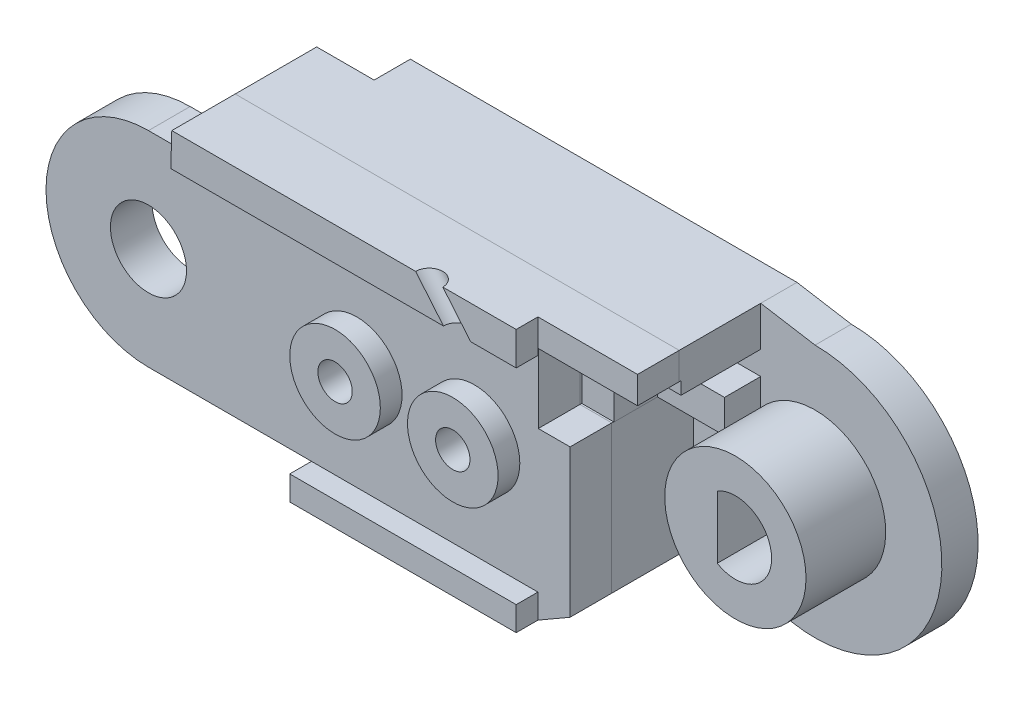
SolidWorks part; units mm, degrees
ref_plane "Front Plane" through (0, 0, 0) normal (0, 0, 1) x (1, 0, 0)
ref_plane "Top Plane" through (0, 0, 0) normal (0, 1, 0) x (1, 0, 0)
ref_plane "Right Plane" through (0, 0, 0) normal (1, 0, 0) x (0, 0, -1)
sketch "Sketch3" plane through (0, 0, 0) normal (0, 0, 1) x (1, 0, 0)
  line L7 (8, 0) -> (9, -2.5)
  line L11 (30, 7) -> (27, 7.5)
  line L13 (0, 7) -> (0, 7.5) construction
  line L14 (0, 7.5) -> (-22.3287, 7.5) construction
  line L15 (0, 5.3) -> (-14, 5.3) construction
  line L16 (0, 4) -> (-14, 4) construction
  line L17 (-14, 4) -> (-14, 5.3) construction
  line L18 (5.6569, 5.6569) -> (5.6569, 7.5)
  line L19 (5.6569, 7.5) -> (27, 7.5)
  line L20 (21.5, -7) -> (9, -7)
  line L21 (9, -7) -> (9, -2.5)
  line L23 (25.0503, -4.9497) -> (21.5, -7)
  arc A4 (8, 0) -> (5.6569, 5.6569) centre (0, 0) ccw
  arc A5 (25.0503, -4.9497) -> (30, 7) centre (30, 0) ccw
  circle A6 centre (0, 0) radius 7 construction
  circle A7 centre (0, 0) radius 3.9 construction
  circle A8 centre (0, 0) radius 5.3 construction
  circle A9 centre (0, 0) radius 4 construction
  dimension "D10" = 0.5
  dimension "D17" = 14
  dimension "D5" = 135
  dimension "D6" = 12.5
  dimension "D7" = 4.5
  dimension "D8" = 1
  dimension "D9" = 45
  dimension "D11" = 1.8431
  dimension "D12" = 30
  dimension "D14" = 3
extrude "Boss-Extrude1" add sketch "Sketch3" along normal blind 2 contours A5 L11 L19 L18 A4 L7 L21 L20 L23
sketch "Sketch20" plane through (0, 0, 0) normal (0, 0, 1) x (1, 0, 0)
  line L0 (0, 7) -> (0, 7.5) construction
  line L1 (0, 7.5) -> (-19.4737, 7.5) construction
  line L2 (0, 5.3) -> (-14, 5.3) construction
  line L3 (0, 4) -> (-14, 4) construction
  line L4 (-14, 4) -> (-14, 5.3) construction
  line L5 (0, 5.3) -> (17.4849, 5.3) construction
  line L6 (17.4849, 5.3) -> (17.4849, 4) construction
  line L7 (17.4849, 4) -> (0, 4) construction
  line L8 (-2.5, 7.5) -> (-2.5, 2.868) construction
  circle A0 centre (0, 0) radius 7 construction
  circle A1 centre (0, 0) radius 3.9 construction
  circle A3 centre (0, 0) radius 5.3 construction
  circle A4 centre (0, 0) radius 4 construction
  circle A5 centre (0, 0) radius 2 construction
  dimension "D1" = 0
  dimension "D2" = 2.5
ref_plane "Plane1" through (0, 0, 2) normal (0, 0, 1) x (1, 0, 0)
sketch "Sketch4" plane through (0, 0, 2) normal (0, 0, 1) x (1, 0, 0)
  line L4 (5.6569, 5.6569) -> (5.6569, 7.5)
  line L5 (5.6569, 5.6569) -> (5.6569, 7.5) construction
  line L6 (5.6569, 7.5) -> (21.5, 7.5)
  line L10 (8, 0) -> (9, -2.5)
  line L11 (9, -2.5) -> (9, -7)
  line L12 (9, -7) -> (21.5, -7)
  line L13 (21.5, -7) -> (21.5, 7.5)
  arc A0 (8, 0) -> (5.6569, 5.6569) centre (0, 0) ccw construction
  arc A3 (8, 0) -> (5.6569, 5.6569) centre (0, 0) ccw
sketch "Sketch22" plane through (0, 0, 2) normal (0, 0, 1) x (1, 0, 0)
  line L0 (5.6569, 5.6569) -> (2.4868, 5.6569)
  line L1 (5.6569, 7.5) -> (21.5, 7.5)
  line L2 (5.6569, 7.5) -> (2.4868, 7.5)
  line L3 (2.4868, 7.5) -> (2.4868, 5.6569)
  line L6 (8, 0) -> (9, -2.5)
  line L7 (9, -2.5) -> (9, -7)
  line L8 (9, -7) -> (21.5, -7)
  line L10 (21.5, 7.5) -> (27, 7.5)
  line L11 (27, 7.5) -> (27, 2.172)
  line L12 (27, 2.172) -> (23.2751, 2.172)
  line L13 (21.5, -7) -> (23.2751, -5.9749)
  line L14 (25.0503, -4.9497) -> (21.5, -7) construction
  line L15 (23.2751, -5.9749) -> (23.2751, 2.172)
  arc A0 (8, 0) -> (5.6569, 5.6569) centre (0, 0) ccw
extrude "Boss-Extrude6" add sketch "Sketch22" along normal blind 4.5
sketch "Sketch25" plane through (0, 0, 2) normal (0, 0, 1) x (1, 0, 0)
  line L0 (0, 5.3) -> (18.0981, 5.3) construction
  line L1 (0, 4) -> (18.0981, 4) construction
  line L2 (18.0981, 4) -> (18.0981, 5.3) construction
sketch "Sketch26" plane through (0, 0, 2) normal (0, 0, 1) x (1, 0, 0)
  line L1 (18.0981, 5.3) -> (2.5301, 5.3)
  line L2 (18.0981, 4) -> (2.5301, 4)
  line L3 (2.5301, 5.3) -> (2.5301, 4)
  line L4 (18.0981, 5.3) -> (27, 5.3)
  line L5 (27, 2.172) -> (27, 7.5) construction
  line L6 (27, 5.3) -> (27, 4)
  line L7 (27, 4) -> (18.0981, 4)
extrude "Cut-Extrude6" cut sketch "Sketch26" along normal blind 4.5
ref_plane "Plane18" through (0, 0, 6.5) normal (0, 0, 1) x (1, 0, 0)
sketch "Sketch31" plane through (0, 0, 6.5) normal (0, 0, 1) x (1, 0, 0)
  line L0 (2.4327, 5.6569) -> (0, 5.6569)
  line L4 (9, -5.6569) -> (0, -5.6569)
  line L5 (2.4327, 5.6569) -> (2.4868, 7.5)
  line L12 (9, -7) -> (9, -5.6569)
  line L13 (9, -2.5) -> (9, -7) construction
  line L16 (27, 7.5) -> (27, 2.172)
  line L17 (27, 2.172) -> (23.2751, 2.172)
  line L18 (23.2751, -5.9749) -> (23.2751, 2.172)
  line L19 (27, 7.5) -> (2.4868, 7.5)
  line L20 (9, -7) -> (21.5, -7)
  line L21 (21.5, -7) -> (23.2751, -5.9749)
  arc A0 (0, 5.6569) -> (0, -5.6569) centre (0, 0) ccw
  dimension "D1" = 5.6569
extrude "Boss-Extrude14" add sketch "Sketch31" along normal blind 2.3 separate body
sketch "Sketch32" plane through (0, 0, 8.8) normal (0, 0, 1) x (1, 0, 0)
  circle A0 centre (0, 0) radius 2.1
extrude "Cut-Extrude7" cut sketch "Sketch32" against normal blind 2.3
sketch "Sketch33" plane through (0, 0, 8.8) normal (0, 0, 1) x (1, 0, 0)
  line L4 (9, -5.6569) -> (9, -7)
  line L11 (9, -7) -> (21.5, -7)
  line L15 (21.5, -7) -> (21.5, -5.6569)
  line L16 (21.5, -5.6569) -> (9, -5.6569)
  line L17 (2.4868, 7.5) -> (21.5, 7.5)
  line L18 (27, 7.5) -> (2.4868, 7.5) construction
  line L19 (2.4868, 7.5) -> (2.4327, 5.6569)
  line L20 (2.4327, 5.6569) -> (21.5, 5.6569)
  line L21 (21.5, 5.6569) -> (21.5, 7.5)
extrude "Boss-Extrude15" add sketch "Sketch33" along normal blind 1.2
sketch "Sketch34" plane through (0, 0, 2) normal (0, 0, 1) x (1, 0, 0)
  line L0 (30, 5.3) -> (18.0981, 5.3) construction
  line L1 (30, 4) -> (18.0981, 4) construction
  circle A0 centre (30, 0) radius 2 construction
  circle A1 centre (30, 0) radius 5.3 construction
  circle A2 centre (30, 0) radius 4 construction
sketch "Sketch35" plane through (0, 0, 8.8) normal (0, 0, 1) x (1, 0, 0)
  line L0 (27, 2.172) -> (27, 6)
  line L1 (27, 2.172) -> (21.5204, 2.172)
  line L2 (27, 6) -> (21.5204, 6)
  line L3 (21.5204, 2.172) -> (21.5204, 6)
  line L4 (27, 2.172) -> (27, 7.5) construction
extrude "Cut-Extrude8" cut sketch "Sketch35" against normal blind 2.4
sketch "Sketch36" plane through (0, 0, 6.4) normal (0, 0, 1) x (1, 0, 0)
  line L0 (27, 2.172) -> (27, 4)
  line L1 (27, 2.172) -> (23.3, 2.172)
  line L2 (27, 4) -> (23.3, 4)
  line L3 (23.3, 2.172) -> (23.3, 4)
  line L4 (21.5, -7) -> (21.5, 7.5) construction
  dimension "D1" = 1.8
extrude "Cut-Extrude9" cut sketch "Sketch36" against normal blind 2.4
sketch "Sketch37" plane through (0, 0, 2) normal (0, 0, 1) x (1, 0, 0)
  circle A0 centre (30, 0) radius 3.9
extrude "Boss-Extrude16" add sketch "Sketch37" along normal blind 4.4
sketch "Sketch39" plane through (0, 0, 6.4) normal (0, 0, 1) x (1, 0, 0)
  line L0 (29, 1.7321) -> (29, -1.7321)
  arc A0 (29, -1.7321) -> (29, 1.7321) centre (30, 0) ccw
  dimension "D2" = 4
  dimension "D1" = 1
extrude "Cut-Extrude10" cut sketch "Sketch39" against normal through all
sketch "Sketch43" plane through (0, 0, 8.8) normal (0, 0, 1) x (1, 0, 0)
  line L2 (0, -5.6569) -> (9, -5.6569) construction
  circle A0 centre (11.5, 0) radius 2.5
  circle A1 centre (18, 0) radius 2.5
  dimension "D1" = 2.5
  dimension "D3" = 5
  dimension "D4" = 6.5
  dimension "D2" = 5.6569
extrude "Boss-Extrude17" add sketch "Sketch43" along normal blind 1.2
sketch "Sketch44" plane through (0, 0, 10) normal (0, 0, 1) x (1, 0, 0)
  circle A0 centre (11.5, 0) radius 0.95
  circle A1 centre (18, 0) radius 0.95
  dimension "D1" = 1.9
  dimension "D2" = 1.9
extrude "Cut-Extrude11" cut sketch "Sketch44" against normal through all
sketch "Sketch45" plane through (0, 0, 0) normal (0, 0, -1) x (-1, 0, 0)
  circle A0 centre (-11.5, 0) radius 2
  circle A1 centre (-18, 0) radius 2
extrude "Cut-Extrude12" cut sketch "Sketch45" against normal blind 4.5
ref_plane "Plane17" through (0, 0, 10) normal (0, 0, 1) x (1, 0, 0)
sketch "Sketch48" plane through (0, 0, 2) normal (0, 0, 1) x (1, 0, 0)
  circle A0 centre (30, 0) radius 5 construction
sketch "Sketch51" plane through (0, 0, 10) normal (0, 0, 1) x (1, 0, 0)
  line L0 (18.2355, 5.6569) -> (27.0112, -4.8677) construction
  line L1 (2.4327, 5.6569) -> (21.5, 5.6569) construction
sketch "Sketch52" plane through (0, 5.6569, 0) normal (0, -1, 0) x (1, 0, 0)
  circle A0 centre (18.2355, 10) radius 0.75
extrude "Cut-Extrude13" cut sketch "Sketch52" along direction (0.6404, -0.768, 0) on the side against the normal blind 10
